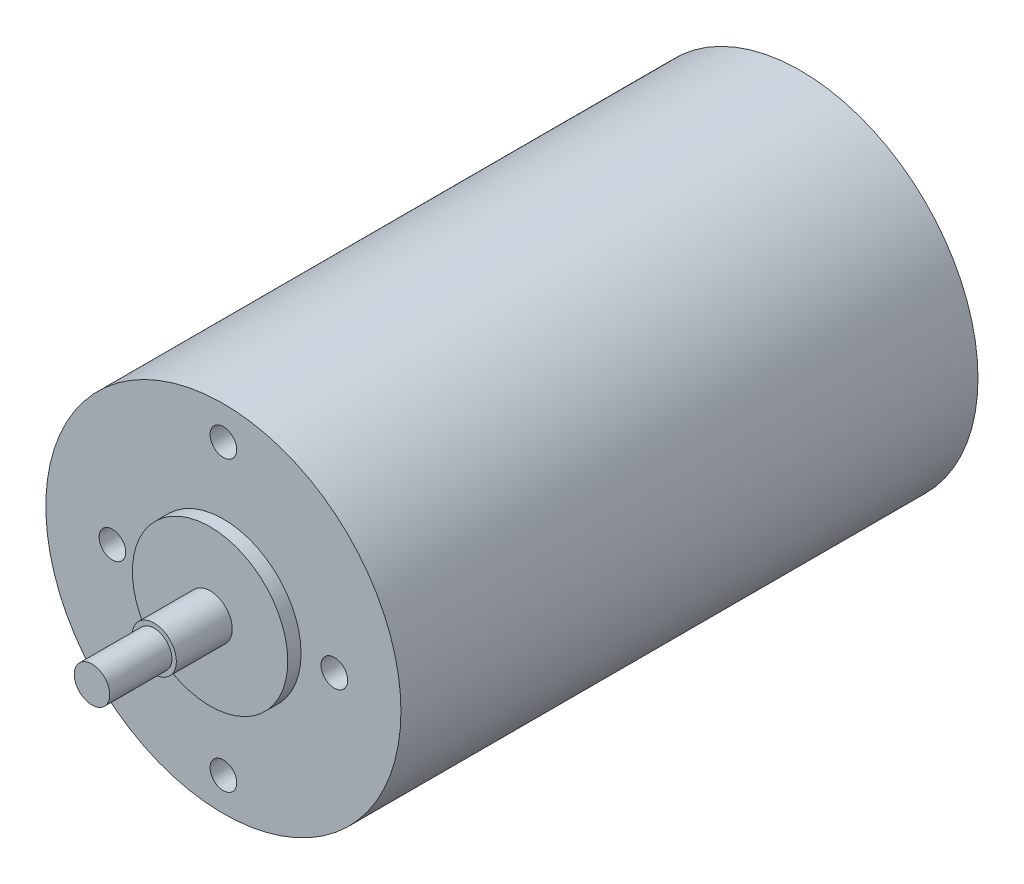
SolidWorks part; units mm, degrees
material "1.5714 (16NiCr4)"
ref_plane "前基準面" through (0, 0, 0) normal (0, 0, 1) x (1, 0, 0)
ref_plane "上基準面" through (0, 0, 0) normal (0, 1, 0) x (1, 0, 0)
ref_plane "右基準面" through (0, 0, 0) normal (1, 0, 0) x (0, 0, -1)
sketch "草圖3" plane through (0, 0, 0) normal (0, 0, 1) x (1, 0, 0)
  circle A0 centre (0, 0) radius 20
  dimension "D1" = 40
extrude "填料-伸長1" add sketch "草圖3" along normal blind 65
sketch "草圖4" plane through (0, 0, 0) normal (0, 0, -1) x (-1, 0, 0)
  circle A0 centre (0, 0) radius 8.75
extrude "填料-伸長2" add sketch "草圖4" along normal blind 1.5
sketch "草圖6" plane through (0, 0, 65) normal (0, 0, 1) x (1, 0, 0)
  circle A0 centre (0, 0) radius 8.75
extrude "填料-伸長3" add sketch "草圖6" along normal blind 1.5
sketch "草圖7" plane through (0, 0, 66.5) normal (0, 0, 1) x (1, 0, 0)
  circle A0 centre (0, 0) radius 2.5
extrude "填料-伸長4" add sketch "草圖7" along normal blind 6.3
sketch "草圖8" plane through (0, 0, 72.8) normal (0, 0, 1) x (1, 0, 0)
  circle A0 centre (0, 0) radius 2
extrude "填料-伸長5" add sketch "草圖8" along normal blind 7
sketch "草圖10" plane through (0, 0, -1.5) normal (0, 0, -1) x (-1, 0, 0)
  circle A0 centre (0, 0) radius 2.5
extrude "填料-伸長6" add sketch "草圖10" along normal blind 1
sketch "草圖11" plane through (0, 0, 65) normal (0, 0, 1) x (1, 0, 0)
  circle A1 centre (-12.5, 0) radius 1.5
  circle A2 centre (12.5, 0) radius 1.5
extrude "除料-伸長1" cut sketch "草圖11" against normal blind 4
sketch "草圖12" plane through (0, 0, 65) normal (0, 0, 1) x (1, 0, 0)
  circle A2 centre (0, 16.25) radius 1.5
  circle A3 centre (0, -16.25) radius 1.5
extrude "除料-伸長2" cut sketch "草圖12" against normal blind 4
